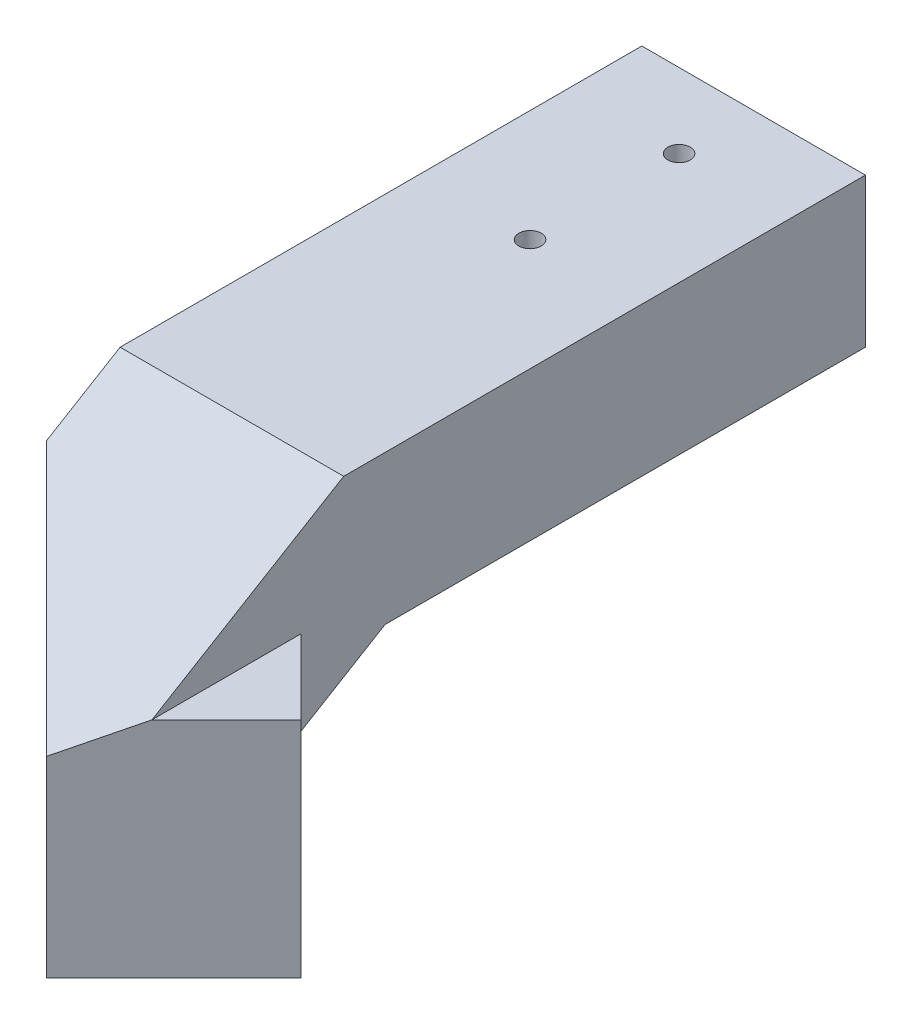
SolidWorks part; units mm, degrees
ref_plane "Alzado" through (0, 0, 0) normal (0, 0, 1) x (1, 0, 0)
ref_plane "Planta" through (0, 0, 0) normal (0, 1, 0) x (1, 0, 0)
ref_plane "Vista lateral" through (0, 0, 0) normal (1, 0, 0) x (0, 0, -1)
sketch "Croquis2" plane through (0, 0, 0) normal (1, 0, 0) x (0, 0, -1)
  line L0 (0, 0) -> (-50, 0)
  line L1 (-50, 0) -> (-75.7248, -15.4349)
  line L2 (-75.7248, -15.4349) -> (-75.7248, -45.4349)
  line L3 (0, -20) -> (-44.4603, -20)
  line L4 (-44.4603, -20) -> (-55.7248, -26.7587)
  line L5 (-55.7248, -26.7587) -> (-55.7248, -45.4349)
  line L6 (-75.7248, -45.4349) -> (-55.7248, -45.4349)
  line L7 (0, -20) -> (0, 0)
  dimension "D1" = 50
  dimension "D2" = 30
  dimension "D3" = 30
  dimension "D4" = 20
extrude "Saliente-Extruir2" add sketch "Croquis2" along normal blind 30
ref_plane "Plano1" through (-22.8624, 0, 22.8624) normal (-0.7071, 0, 0.7071) x (0.7071, 0, 0.7071)
sketch "Croquis3" plane through (-22.8624, 0, 22.8624) normal (-0.7071, 0, 0.7071) x (0.7071, 0, 0.7071)
  line L1 (81.8312, 10.6133) -> (21.2018, 10.6133)
  line L2 (81.8312, 10.6133) -> (81.8312, -50.3524)
  line L3 (81.8312, -50.3524) -> (21.2018, -50.3524)
  line L4 (21.2018, 10.6133) -> (21.2018, -50.3524)
extrude "Cortar-Extruir1" cut sketch "Croquis3" along normal blind 30
sketch "Croquis4" plane through (-22.8624, 0, 22.8624) normal (-0.7071, 0, 0.7071) x (0.7071, 0, 0.7071)
  circle A0 centre (60.6166, -34.2261) radius 3
  dimension "D1" = 6
extrude "Cortar-Extruir2" cut sketch "Croquis4" against normal through all
sketch "Croquis5" plane through (-22.8624, 0, 22.8624) normal (-0.7071, 0, 0.7071) x (0.7071, 0, 0.7071)
  line L1 (46.4744, -45.4349) -> (74.7587, -45.4349)
  line L2 (46.4744, -45.4349) -> (46.4744, -15.4349)
  line L3 (46.4744, -15.4349) -> (74.7587, -15.4349)
  line L4 (74.7587, -45.4349) -> (74.7587, -15.4349)
  line L5 (74.7587, -15.4349) -> (74.7587, -45.4349) construction
extrude "Saliente-Extruir3" add sketch "Croquis5" against normal up to vertex (14.1421 mm away)
sketch "Croquis6" plane through (-22.8624, 0, 22.8624) normal (-0.7071, 0, 0.7071) x (0.7071, 0, 0.7071)
  line L7 (32.3323, -20.7587) -> (46.4744, -26.7587)
  line L8 (46.4744, -26.7587) -> (46.4744, -45.4349)
  line L9 (46.4744, -45.4349) -> (74.7587, -45.4349)
  line L10 (74.7587, -45.4349) -> (74.7587, -15.4349)
  line L11 (74.7587, -15.4349) -> (38.3784, 0)
  line L12 (38.3784, 0) -> (32.3323, 0)
  line L13 (32.3323, 0) -> (32.3323, -20.7587)
  line L14 (32.3323, -20.7587) -> (46.4744, -26.7587)
  line L15 (46.4744, -26.7587) -> (46.4744, -45.4349)
  line L16 (46.4744, -45.4349) -> (74.7587, -45.4349)
  line L17 (74.7587, -45.4349) -> (74.7587, -15.4349)
  line L18 (74.7587, -15.4349) -> (38.3784, 0)
  line L19 (38.3784, 0) -> (32.3323, 0)
  line L20 (32.3323, 0) -> (32.3323, -20.7587)
  dimension "D1" = 0
extrude "Saliente-Extruir4" add sketch "Croquis6" along normal blind 10
sketch "Croquis7" plane through (0, 0, 0) normal (0, 1, 0) x (1, 0, 0)
  line L0 (0, 0) -> (0, -45.7248) construction
  line L1 (0, -42.9549) -> (-23.5817, -42.9549)
  line L2 (0, -42.9549) -> (0, -73.1611)
  line L3 (0, -73.1611) -> (-23.5817, -73.1611)
  line L4 (-23.5817, -42.9549) -> (-23.5817, -73.1611)
extrude "Cortar-Extruir3" cut sketch "Croquis7" against normal blind 60
sketch "Croquis8" plane through (-29.9335, 0, 29.9335) normal (-0.7071, 0, 0.7071) x (0.7071, 0, 0.7071)
  line L0 (60.6166, -45.4349) -> (60.6166, -35.4349) construction
  line L1 (46.4744, -45.4349) -> (74.7587, -45.4349) construction
  circle A0 centre (60.6166, -35.4349) radius 3
  dimension "D1" = 10
  dimension "D2" = 6
extrude "Cortar-Extruir4" cut sketch "Croquis8" against normal through all
ref_plane "Plano2" through (30, 0, 50) normal (-1, 0, 0) x (0, 0, 1)
sketch "Croquis10" plane through (0, 22.0588, 13.2353) normal (0, 0.8575, 0.5145) x (1, 0, 0)
  line L1 (47.0599, -40.39) -> (-32.0125, -40.39)
  line L2 (47.0599, -40.39) -> (47.0599, -96.7913)
  line L3 (47.0599, -96.7913) -> (-32.0125, -96.7913)
  line L4 (-32.0125, -40.39) -> (-32.0125, -96.7913)
extrude "Cortar-Extruir5" cut sketch "Croquis10" along normal blind 50
sketch "Croquis12" plane through (0, 0, 0) normal (0, 0, -1) x (-1, 0, 0)
  line L4 (0, -20) -> (0, 0)
  line L5 (0, 0) -> (-30, 0)
  line L6 (-30, 0) -> (-30, -20)
  line L7 (-30, -20) -> (0, -20)
  line L8 (0, -20) -> (0, 0)
  line L9 (0, 0) -> (-30, 0)
  line L10 (-30, 0) -> (-30, -20)
  line L11 (-30, -20) -> (0, -20)
  dimension "D1" = 0
extrude "Saliente-Extruir6" add sketch "Croquis12" along normal blind 20
sketch "Croquis13" plane through (0, -20, 0) normal (0, -1, 0) x (1, 0, 0)
  line L0 (15, -20) -> (15, 19.6739) construction
  line L1 (30, -20) -> (0, -20) construction
  circle A0 centre (15, -10) radius 1.5
  circle A1 centre (15, 10) radius 1.5
  dimension "D1" = 3
  dimension "D2" = 3
  dimension "D3" = 10
  dimension "D4" = 30
extrude "Cortar-Extruir6" cut sketch "Croquis13" against normal blind 20
move or copy body "Sólido-Mover/Copiar1" [suppressed] bodies to move or copy 113
